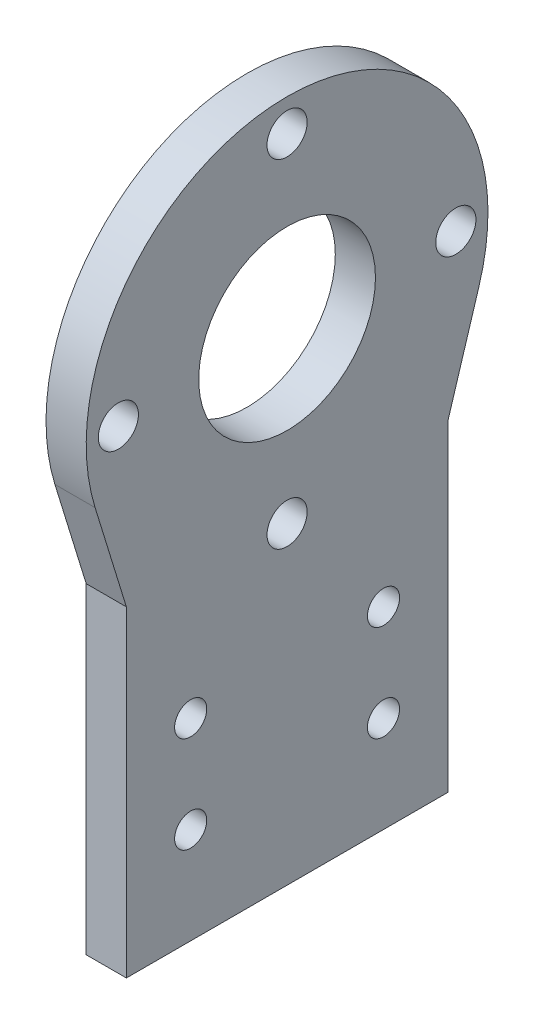
SolidWorks part; units mm, degrees
ref_plane "Alzado" through (0, 0, 0) normal (0, 0, 1) x (1, 0, 0)
ref_plane "Planta" through (0, 0, 0) normal (0, 1, 0) x (1, 0, 0)
ref_plane "Vista lateral" through (0, 0, 0) normal (1, 0, 0) x (0, 0, -1)
sketch "Croquis1" plane through (0, 0, 0) normal (1, 0, 0) x (0, 0, -1)
  line L0 (0, 0) -> (0, 40)
  line L1 (0, 40) -> (40, 40)
  line L2 (40, 40) -> (40, 0)
  line L3 (20, 40) -> (20, 60) construction
  line L4 (0, 0) -> (40, 0)
  line L5 (8, 24) -> (8, 12) construction
  line L6 (0, 40) -> (-3.893, 52.643)
  line L7 (40, 40) -> (43.893, 52.643)
  line L8 (8, 24) -> (32, 24) construction
  line L9 (8, 12) -> (32, 12) construction
  line L10 (32, 12) -> (32, 24) construction
  circle A0 centre (20, 60) radius 25
  circle A1 centre (20, 60) radius 11
  circle A2 centre (8, 24) radius 2
  circle A3 centre (8, 12) radius 2
  circle A4 centre (32, 12) radius 2
  circle A5 centre (32, 24) radius 2
  circle A6 centre (20, 60) radius 21 construction
  circle A7 centre (20, 81) radius 2.5
  circle A8 centre (41, 60) radius 2.5
  circle A9 centre (20, 39) radius 2.5
  circle A10 centre (-1, 60) radius 2.5
  point P31 (20, 60)
  dimension "D2" = 50
  dimension "D4" = 22
  dimension "D7" = 4
  dimension "D12" = 42
  dimension "D13" = 5
  dimension "D1" = 40
  dimension "D3" = 20
  dimension "D5" = 90
  dimension "D6" = 90
  dimension "D8" = 12
  dimension "D9" = 12
  dimension "D10" = 8
  dimension "D11" = 40
  dimension "D14" = 4
extrude "Saliente-Extruir1" add sketch "Croquis1" along normal blind 5 contours A0 L1 A1 | A0 L1 L0 L4 L2 A4 A3 A2 A5 | L1 A0 | A0 L6 L1 | A0 L1 L7
sketch "Croquis2" plane through (5, 0, 0) normal (1, 0, 0) x (0, 0, -1)
  line L5 (40, 0) -> (40, 40)
  line L6 (40, 40) -> (43.893, 52.643)
  line L7 (-3.893, 52.643) -> (0, 40)
  line L8 (0, 40) -> (0, 0)
  line L9 (0, 0) -> (40, 0)
  line L10 (40, 0) -> (40, 40)
  line L11 (40, 40) -> (43.893, 52.643)
  line L12 (-3.893, 52.643) -> (0, 40)
  line L13 (0, 40) -> (0, 0)
  line L14 (0, 0) -> (40, 0)
  circle A0 centre (32, 12) radius 2 construction
  arc A1 (43.893, 52.643) -> (-3.893, 52.643) centre (20, 60) ccw
  arc A2 (43.893, 52.643) -> (-3.893, 52.643) centre (20, 60) ccw
  circle A3 centre (32, 24) radius 2 construction
  circle A4 centre (8, 12) radius 2 construction
  circle A5 centre (8, 24) radius 2 construction
  circle A6 centre (20, 39) radius 2.5 construction
  circle A7 centre (41, 60) radius 2.5 construction
  circle A8 centre (20, 81) radius 2.5 construction
  circle A9 centre (20, 60) radius 11 construction
  circle A10 centre (-1, 60) radius 2.5 construction
  circle A11 centre (32, 12) radius 2
  circle A12 centre (32, 24) radius 2
  circle A13 centre (8, 12) radius 2
  circle A14 centre (8, 24) radius 2
  circle A15 centre (20, 39) radius 2.5
  circle A16 centre (41, 60) radius 2.5
  circle A17 centre (20, 81) radius 2.5
  circle A18 centre (20, 60) radius 11
  circle A19 centre (-1, 60) radius 2.5
  dimension "D1" = 0
